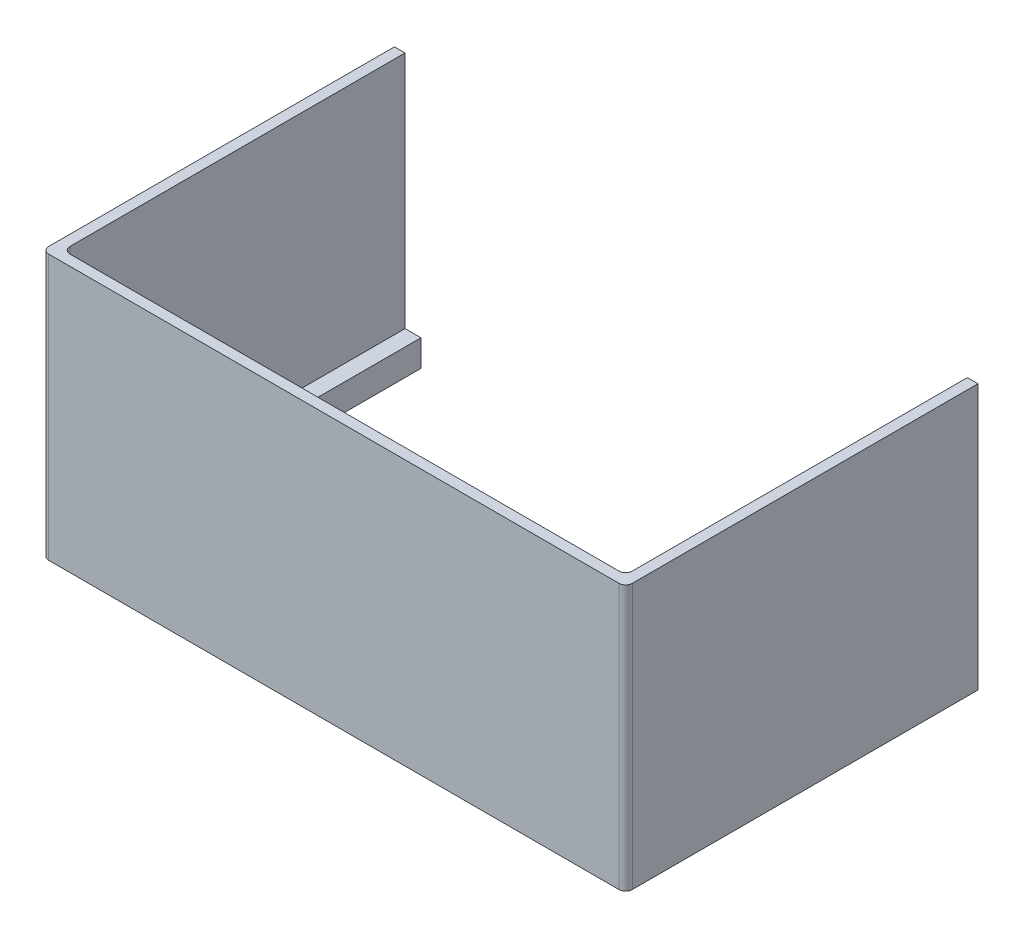
SolidWorks part; units mm, degrees
ref_plane "Front Plane" through (0, 0, 0) normal (0, 0, 1) x (1, 0, 0)
ref_plane "Top Plane" through (0, 0, 0) normal (0, 1, 0) x (1, 0, 0)
ref_plane "Right Plane" through (0, 0, 0) normal (1, 0, 0) x (0, 0, -1)
sketch "Sketch1" plane through (0, 0, 0) normal (0, 1, 0) x (1, 0, 0)
  line L1 (-69.85, -77.1042) -> (69.85, -77.1042)
  line L2 (-69.85, -77.1042) -> (-69.85, 77.1042)
  line L3 (-69.85, 77.1042) -> (69.85, 77.1042)
  line L4 (69.85, -77.1042) -> (69.85, 77.1042)
  line L5 (-69.85, -77.1042) -> (69.85, 77.1042) construction
  line L6 (-69.85, 77.1042) -> (69.85, -77.1042) construction
  point P0 (0, 0)
  dimension "D1" = 154.2085
  dimension "D2" = 139.7
extrude "Boss-Extrude1" add sketch "Sketch1" along normal blind 6.35
sketch "Sketch2" plane through (0, 6.35, 0) normal (0, 1, 0) x (1, 0, 0)
  line L0 (69.85, 77.1042) -> (-69.85, 77.1042) construction
  line L1 (-63.5, -70.7542) -> (63.5, -70.7542)
  line L2 (-63.5, -70.7542) -> (-63.5, 70.7542)
  line L3 (-63.5, 70.7542) -> (63.5, 70.7542)
  line L4 (63.5, -70.7542) -> (63.5, 70.7542)
  line L5 (-63.5, -70.7542) -> (63.5, 70.7542) construction
  line L6 (-63.5, 70.7542) -> (63.5, -70.7542) construction
  line L7 (69.85, -77.1042) -> (69.85, 77.1042) construction
  point P0 (0, 0)
  dimension "D1" = 6.35
  dimension "D2" = 6.35
extrude "Cut-Extrude1" cut sketch "Sketch2" against normal blind 6.35
sketch "Sketch3" plane through (0, 6.35, 0) normal (0, 1, 0) x (1, 0, 0)
  line L1 (-69.85, 77.1042) -> (69.85, 77.1042)
  line L2 (-69.85, 77.1042) -> (-69.85, -77.1042)
  line L3 (-69.85, -77.1042) -> (69.85, -77.1042)
  line L4 (69.85, 77.1042) -> (69.85, -77.1042)
  line L5 (-69.85, 77.1042) -> (69.85, -77.1042) construction
  line L6 (-69.85, -77.1042) -> (69.85, 77.1042) construction
  line L7 (-67.31, 74.5642) -> (67.31, 74.5642)
  line L8 (-67.31, 74.5642) -> (-67.31, -74.5642)
  line L9 (-67.31, -74.5642) -> (67.31, -74.5642)
  line L10 (67.31, 74.5642) -> (67.31, -74.5642)
  line L11 (-67.31, 74.5642) -> (67.31, -74.5642) construction
  line L12 (-67.31, -74.5642) -> (67.31, 74.5642) construction
  point P0 (0, 0)
  point P7 (0, 0)
  dimension "D1" = 2.54
  dimension "D2" = 2.54
extrude "Boss-Extrude2" add sketch "Sketch3" along normal blind 57.15
sketch "Sketch4" plane through (0, 63.5, 0) normal (0, 1, 0) x (1, 0, 0)
  line L1 (-69.85, 77.1042) -> (69.85, 77.1042)
  line L2 (-69.85, 77.1042) -> (-69.85, 7.2542)
  line L3 (-69.85, 7.2542) -> (69.85, 7.2542)
  line L4 (69.85, 77.1042) -> (69.85, 7.2542)
  dimension "D1" = 69.85
extrude "Cut-Extrude2" cut sketch "Sketch4" against normal through all contours L3 L4 L1 L2
sketch "Sketch5" plane through (0, 0, -7.2542) normal (0, 0, -1) x (-1, 0, 0)
  line L0 (-67.31, 6.35) -> (-67.31, 63.5) construction
  line L1 (-67.437, 4.8895) -> (-64.9605, 4.8895)
  line L2 (-67.437, 4.8895) -> (-67.437, 1.4605)
  line L3 (-67.437, 1.4605) -> (-64.9605, 1.4605)
  line L4 (-64.9605, 4.8895) -> (-64.9605, 1.4605)
  line L5 (-67.31, 6.35) -> (-63.5, 6.35) construction
  line L6 (-63.5, 0) -> (-69.85, 0) construction
  line L7 (-63.5, 0) -> (-63.5, 6.35) construction
  line L8 (0, 0) -> (0, 25.1433) construction
  line L9 (63.5, 0) -> (-63.5, 0) construction
  line L10 (64.9605, 4.8895) -> (64.9605, 1.4605)
  line L11 (67.437, 1.4605) -> (64.9605, 1.4605)
  line L12 (67.437, 4.8895) -> (67.437, 1.4605)
  line L13 (67.437, 4.8895) -> (64.9605, 4.8895)
  dimension "D1" = 0.127
  dimension "D2" = 1.4605
  dimension "D3" = 1.4605
  dimension "D4" = 1.4605
extrude "Cut-Extrude3" cut sketch "Sketch5" against normal blind 3.81 contours L12 L13 L10 L11 | L1 L4 L3 L2
fillet "Fillet1" radius 1.5875 4 edges at (69.85, 31.75, 77.1042) (-69.85, 31.75, 77.1042) (-67.31, 34.925, 74.5642) (67.31, 34.925, 74.5642)
